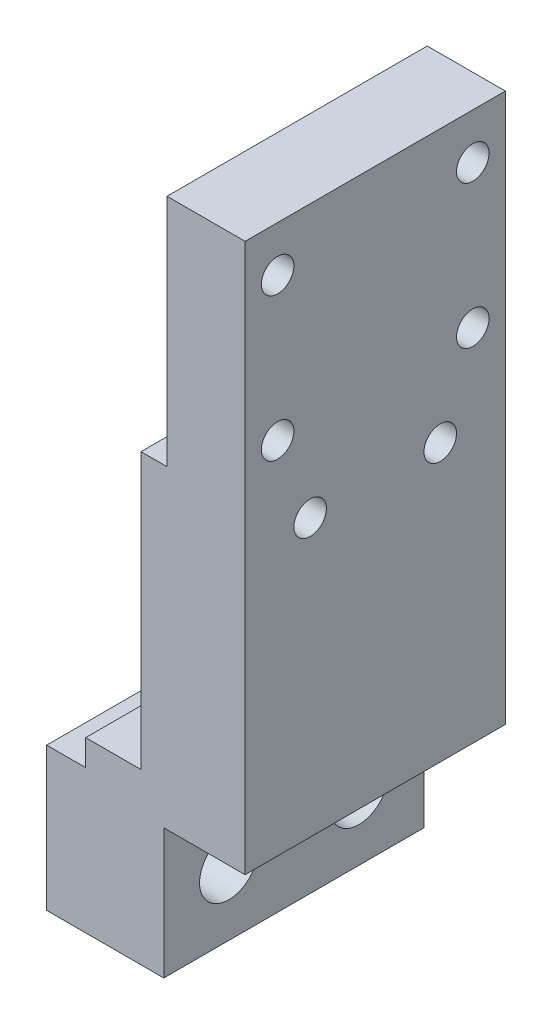
SolidWorks part; units mm, degrees
ref_plane "前视基准面" through (0, 0, 0) normal (0, 0, 1) x (1, 0, 0)
ref_plane "上视基准面" through (0, 0, 0) normal (0, 1, 0) x (1, 0, 0)
ref_plane "右视基准面" through (0, 0, 0) normal (1, 0, 0) x (0, 0, -1)
sketch "草图1" plane through (0, 0, 0) normal (0, 0, 1) x (1, 0, 0)
  line L0 (-6, 13) -> (-1.75, 13)
  line L1 (-1.75, 34.16) -> (-1.75, 13)
  line L2 (0.25, 34.16) -> (-1.75, 34.16)
  line L3 (0.25, 34.16) -> (0.25, 52.16)
  line L4 (0.25, 52.16) -> (6.25, 52.16)
  line L5 (6.25, 10) -> (6.25, 52.16)
  line L6 (0, 10) -> (6.25, 10)
  line L7 (0, 10) -> (0, 0)
  line L8 (0, 0) -> (-9, 0)
  line L9 (-9, 0) -> (-9, 11)
  line L10 (-6, 11) -> (-9, 11)
  line L11 (-6, 11) -> (-6, 13)
  line L12 (-4.6, 5) -> (-4.6, 9) construction
  line L13 (-4.6, 1) -> (-4.6, 5) construction
  line L14 (-9, 1) -> (-4.6, 1) construction
  line L15 (-4.6, 9) -> (-9, 9) construction
  line L20 (-4.6, 2.75) -> (0, 2.75) construction
  line L21 (0, 7.25) -> (-4.6, 7.25) construction
  line L22 (6.25, 32.5) -> (-1.75, 32.5) construction
extrude "凸台-拉伸1" add sketch "草图1" along normal blind 20
hole_wizard "M3 螺纹孔1" positions "草图2" profile "草图3" tap size "M3" standard "ISO"
sketch "草图2" plane through (6.25, 0, 0) normal (1, 0, 0) x (0, 0, -1)
  line L0 (-10, 52.16) -> (-10, 2.7857) construction
  line L1 (-20, 52.16) -> (0, 52.16) construction
  point P2 (-2.5, 48.66)
  point P4 (-2.5, 37.66)
  point P8 (-5, 31.26)
  point P18 (0, 0)
  point P19 (-15, 31.26)
  point P20 (-17.5, 37.66)
  point P21 (-17.5, 48.66)
  dimension "D1" = 3.5
  dimension "D2" = 14.5
  dimension "D3" = 20.9
  dimension "D4" = 10
  dimension "D5" = 15
sketch "草图3" plane through (6.25, 48.66, 2.5) normal (0, 1, 0) x (0, 0, -1)
  line L0 (0, 0) -> (0, 10.2511)
  line L1 (0, 10.2511) -> (1.25, 9.5)
  line L2 (1.25, 9.5) -> (1.25, 0)
  line L5 (1.25, 0) -> (0, 0)
  line L10 (0, 10.2511) -> (-1.25, 9.5) construction
  line L11 (0, -6.35) -> (0, 107.95) construction
  dimension "螺纹孔钻头直径" = 2.5
  dimension "螺纹孔钻头深度" = 9.5
  dimension "导头角度" = 118
cosmetic thread "孔螺蚊线1" parameters "D1"=6, "D2"=3
cosmetic thread "孔螺蚊线2" parameters "D1"=6, "D2"=3
cosmetic thread "孔螺蚊线3" parameters "D1"=8, "D2"=3
cosmetic thread "孔螺蚊线4" parameters "D1"=8, "D2"=3
cosmetic thread "孔螺蚊线5" parameters "D1"=6, "D2"=3
cosmetic thread "孔螺蚊线6" parameters "D1"=6, "D2"=3
hole_wizard "M4 六角凹头螺钉的柱形沉头孔1" positions "草图6" profile "草图7" counterbore size "M4" standard "ISO"
sketch "草图6" plane through (-9, 0, 0) normal (-1, 0, 0) x (0, 0, 1)
  line L0 (10, 0) -> (10, 26.6431) construction
  line L1 (20, 0) -> (0, 0) construction
  line L3 (20, 52.16) -> (0, 52.16) construction
  point P0 (5, 4.96)
  point P2 (15, 4.96)
  point P11 (0, 0)
  dimension "D1" = 10
  dimension "D2" = 47.2
sketch "草图7" plane through (-9, 4.96, 5) normal (0, 1, 0) x (0, 0, 1)
  line L0 (0, 0) -> (0, 10.8519)
  line L1 (0, 10.8519) -> (2.25, 9.5)
  line L2 (2.25, 9.5) -> (2.25, 4.4)
  line L3 (2.25, 4.4) -> (4, 4.4)
  line L4 (4, 4.4) -> (4, 0)
  line L5 (4, 0) -> (0, 0)
  line L10 (0, 10.8519) -> (-2.25, 9.5) construction
  line L11 (0, -6.35) -> (0, 107.95) construction
  dimension "孔直径" = 4.5
  dimension "孔深度" = 9.5
  dimension "柱形沉头孔直径" = 8
  dimension "柱形沉头孔深度" = 4.4
  dimension "导头角度" = 118
